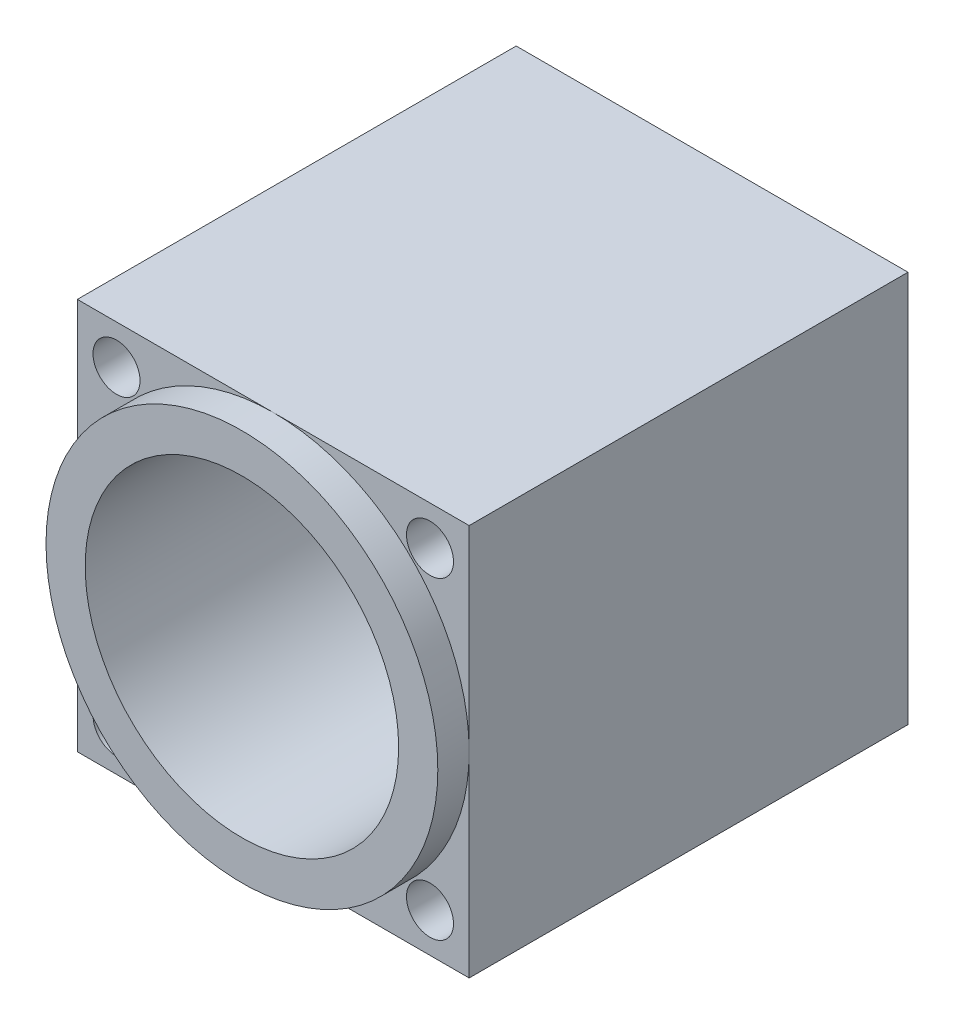
SolidWorks part; units mm, degrees
ref_plane "Plan de face" through (0, 0, 0) normal (0, 0, 1) x (1, 0, 0)
ref_plane "Plan de dessus" through (0, 0, 0) normal (0, 1, 0) x (1, 0, 0)
ref_plane "Plan de droite" through (0, 0, 0) normal (1, 0, 0) x (0, 0, -1)
sketch "Esquisse1" plane through (0, 0, 0) normal (0, 0, 1) x (1, 0, 0)
  line L0 (12.5, -12.5) -> (12.5, 12.5)
  line L1 (-12.5, 12.5) -> (12.5, 12.5)
  line L2 (-10, -10) -> (10, -10) construction
  line L3 (-12.5, -12.5) -> (-12.5, 12.5)
  line L6 (-12.5, -12.5) -> (12.5, -12.5)
  circle A0 centre (10, 10) radius 1.5
  circle A1 centre (0, 0) radius 3
  circle A2 centre (-10, 10) radius 1.5
  circle A3 centre (10, -10) radius 1.5
  circle A4 centre (-10, -10) radius 1.5
  dimension "D1" = 12.5
  dimension "D2" = 20
  dimension "D3" = 20
  dimension "D4" = 10
  dimension "D5" = 20
extrude "Extrusion3" add sketch "Esquisse1" along normal blind 30
sketch "Esquisse7" plane through (0, 0, 30) normal (0, 0, 1) x (1, 0, 0)
  circle A0 centre (0, 0) radius 10
sketch "Esquisse8" plane through (0, 0, 30) normal (0, 0, 1) x (1, 0, 0)
  circle A0 centre (0, 0) radius 10
extrude "Extrusion4" cut sketch "Esquisse8" against normal blind 28
sketch "Esquisse10" plane through (0, 0, 30) normal (0, 0, 1) x (1, 0, 0)
  circle A0 centre (0, 0) radius 12.5
  circle A1 centre (0, 0) radius 18.0494
extrude "Extrusion6" cut sketch "Esquisse10" against normal blind 2
